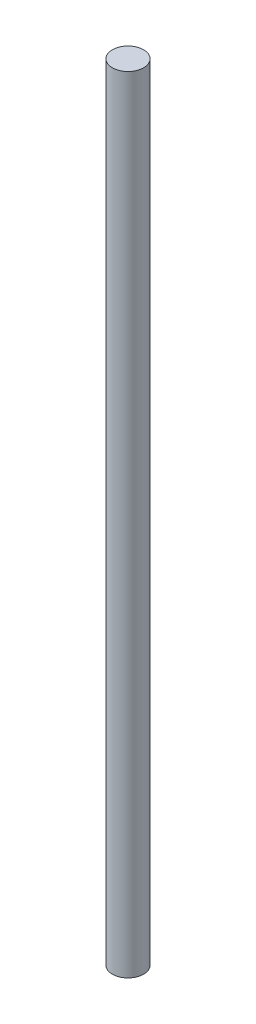
SolidWorks part; units mm, degrees
ref_plane "Front Plane" through (0, 0, 0) normal (0, 0, 1) x (1, 0, 0)
ref_plane "Top Plane" through (0, 0, 0) normal (0, 1, 0) x (1, 0, 0)
ref_plane "Right Plane" through (0, 0, 0) normal (1, 0, 0) x (0, 0, -1)
sketch "Sketch1" plane through (0, 0, 0) normal (0, 0, 1) x (1, 0, 0)
  line L0 (0, 0) -> (0, 239)
  line L1 (0, 0) -> (4.7625, 0)
  line L2 (0, 239) -> (4.7625, 239)
  line L4 (4.7625, 239) -> (4.7625, 0) construction
  line L5 (4.7625, 239) -> (4.7625, 0)
  dimension "D1" = 4.7625
  dimension "D2" = 239
revolve "Revolve1" add sketch "Sketch1" angle 360 about L4
